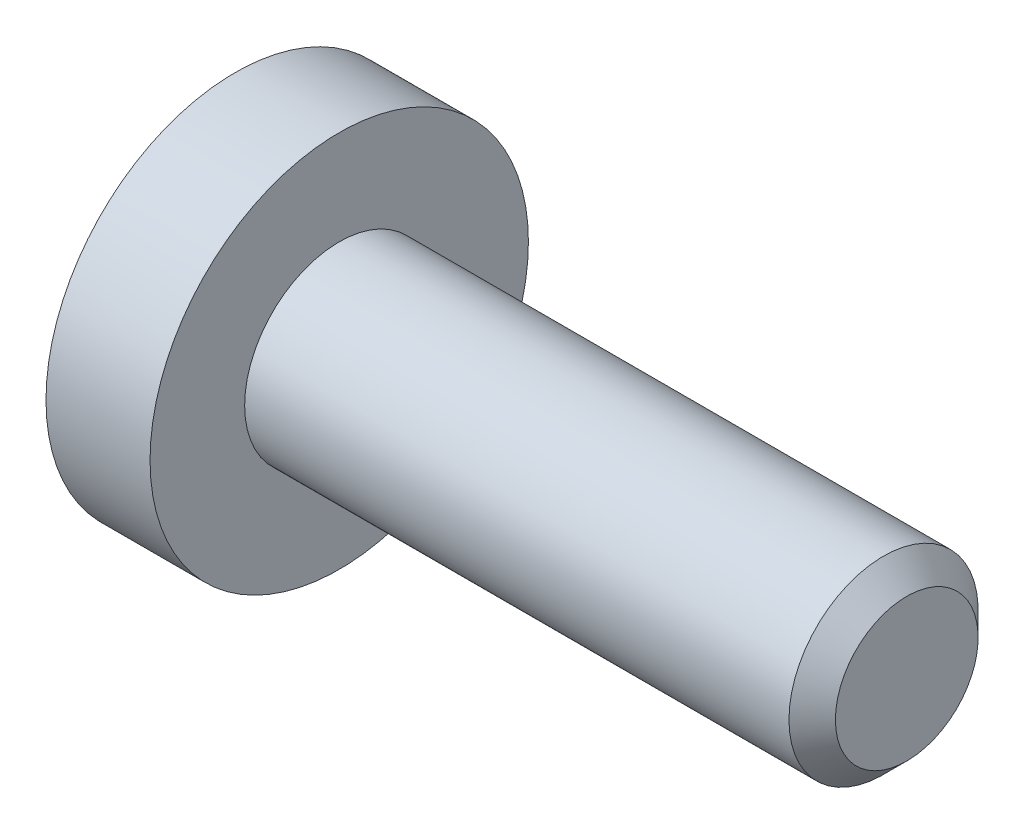
SolidWorks part; units mm, degrees
material "AISI 304"
ref_plane "正面" through (0, 0, 0) normal (0, 0, 1) x (1, 0, 0)
ref_plane "平面" through (0, 0, 0) normal (0, 1, 0) x (1, 0, 0)
ref_plane "右側面" through (0, 0, 0) normal (1, 0, 0) x (0, 0, -1)
ref_plane "Plane1" through (0, 0, 0) normal (0, 0, 1) x (1, 0, 0)
sketch "Sketch1" plane through (0, 0, 0) normal (0, 0, 1) x (1, 0, 0)
  line L0 (-1.1, 0) -> (-1.1, 2)
  line L1 (-1.1, 2) -> (0, 2)
  line L2 (0, 2) -> (0, 1)
  line L3 (0, 1) -> (5.7545, 1)
  line L4 (5.7545, 1) -> (6, 0.7545)
  line L5 (6, 0.7545) -> (6, 0)
  line L6 (6, 0) -> (-1.1, 0)
  line L7 (6, 0) -> (-1.1, 0) construction
revolve "Revolve1" add sketch "Sketch1" angle 360 about L7
cosmetic thread "Cosmetic Thread1" parameters "D1"=5.5748, "D2"=1.509
ref_plane "Plane2" through (-1.1, 0, 0) normal (1, 0, 0) x (0, 0, -1)
sketch "Sketch2" plane through (-1.1, 0, 0) normal (1, 0, 0) x (0, 0, -1)
  line L0 (-0.65, -0.3753) -> (0, -0.7506)
  line L1 (0, -0.7506) -> (0.65, -0.3753)
  line L2 (0.65, -0.3753) -> (0.65, 0.3753)
  line L3 (0.65, 0.3753) -> (0, 0.7506)
  line L4 (0, 0.7506) -> (-0.65, 0.3753)
  line L5 (-0.65, 0.3753) -> (-0.65, -0.3753)
extrude "Cut-Extrude1" cut sketch "Sketch2" along normal blind 1.2
